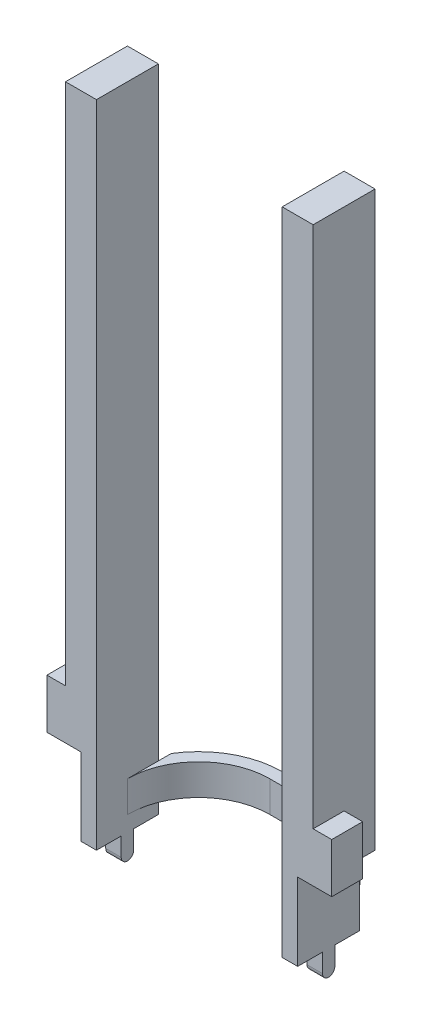
SolidWorks part; units mm, degrees
ref_plane "Front" through (0, 0, 0) normal (0, 0, 1) x (1, 0, 0)
ref_plane "Top" through (0, 0, 0) normal (0, 1, 0) x (1, 0, 0)
ref_plane "Right" through (0, 0, 0) normal (1, 0, 0) x (0, 0, -1)
sketch "草图2" plane through (0, 0, 0) normal (0, 1, 0) x (1, 0, 0)
  line L1 (-7, 23) -> (7, 23)
  line L4 (-7, 27) -> (7, 27)
  line L6 (-38.2984, -16) -> (-23.5227, -16) construction
  line L8 (-35.4759, -14) -> (-25.2483, -14) construction
  line L10 (25.2483, -14) -> (35.6561, -14) construction
  line L11 (23.5227, -16) -> (40.8516, -16) construction
  line L12 (-34, 0) -> (-30, 0)
  line L14 (30, 0) -> (34, 0)
  arc A4 (-7, 27) -> (-34, 0) centre (-7, 0) ccw
  arc A8 (-7, 23) -> (-30, 0) centre (-7, 0) ccw
  arc A10 (30, 0) -> (7, 23) centre (7, 0) ccw
  arc A11 (34, 0) -> (7, 27) centre (7, 0) ccw
  point P3 (0, 0)
  point P10 (0, 0)
extrude "凸台-拉伸1" add sketch "草图2" along normal blind 10
sketch "草图3" plane through (0, 10, 0) normal (0, 1, 0) x (1, 0, 0)
  line L1 (-30, 10) -> (-40, 10)
  line L2 (-30, 10) -> (-30, -10)
  line L3 (-30, -10) -> (-40, -10)
  line L4 (-40, 10) -> (-40, -10)
  line L5 (30, 10) -> (40, 10)
  line L6 (30, 10) -> (30, -10)
  line L7 (30, -10) -> (40, -10)
  line L8 (40, 10) -> (40, -10)
  dimension "D1" = 60
  dimension "D2" = 10
  dimension "D3" = 10
  dimension "D4" = 20
  dimension "D5" = 10
  dimension "D6" = 20
  dimension "D7" = 10
extrude "凸台-拉伸2" add sketch "草图3" along normal mid plane 30
sketch "草图4" plane through (40, 0, 0) normal (1, 0, 0) x (0, 0, -1)
  line L5 (-10, -5) -> (10, -5) construction
  line L6 (-2, -5) -> (2, -5)
  line L7 (-2, -5) -> (-2, -11)
  line L9 (2, -5) -> (2, -11)
  arc A1 (-2, -11) -> (2, -11) centre (0, -11) ccw
  dimension "D3" = 2
extrude "凸台-拉伸3" add sketch "草图4" against normal blind 10
sketch "草图5" plane through (-40, 0, 0) normal (-1, 0, 0) x (0, 0, 1)
  line L0 (-10, -5) -> (10, -5) construction
  line L14 (-2, -5) -> (2, -5)
  line L15 (-2, -5) -> (-2, -11)
  line L17 (2, -5) -> (2, -11)
  line L18 (0, 0) -> (0, -16.9384) construction
  arc A2 (-2, -11) -> (2, -11) centre (0, -11) ccw
  dimension "D3" = 2
extrude "凸台-拉伸4" add sketch "草图5" against normal blind 10
sketch "草图6" plane through (0, 25, 0) normal (0, 1, 0) x (1, 0, 0)
  line L1 (-40, 10) -> (-30, 10)
  line L2 (-40, 10) -> (-40, -10)
  line L3 (-40, -10) -> (-30, -10)
  line L4 (-30, 10) -> (-30, -10)
  line L5 (30, 10) -> (40, 10)
  line L6 (30, 10) -> (30, -10)
  line L7 (30, -10) -> (40, -10)
  line L8 (40, 10) -> (40, -10)
extrude "凸台-拉伸5" add sketch "草图6" along normal blind 180
sketch "草图7" plane through (0, -5, 0) normal (0, -1, 0) x (1, 0, 0)
  line L1 (-30, -10) -> (-40.3792, -10)
  line L2 (-30, -10) -> (-30, -20.8781)
  line L3 (-30, -20.8781) -> (-40.3792, -20.8781)
  line L4 (-40.3792, -10) -> (-40.3792, -20.8781)
  line L5 (30, -10) -> (37.1745, -10)
  line L6 (30, -10) -> (30, -21.5992)
  line L7 (30, -21.5992) -> (37.1745, -21.5992)
  line L8 (37.1745, -10) -> (37.1745, -21.5992)
extrude "切除-拉伸1" cut sketch "草图7" against normal through all
sketch "草图8" plane through (0, -5, 0) normal (0, -1, 0) x (1, 0, 0)
  line L0 (-30, -10) -> (-40, -10) construction
  line L1 (-40, 10) -> (-35, 10)
  line L2 (-40, 10) -> (-40, -10)
  line L3 (-40, -10) -> (-35, -10)
  line L4 (-35, 10) -> (-35, -10)
  line L5 (40, -10) -> (30, -10) construction
  line L6 (40, 10) -> (35, 10)
  line L7 (40, 10) -> (40, -10)
  line L8 (40, -10) -> (35, -10)
  line L9 (35, 10) -> (35, -10)
extrude "切除-拉伸2" cut sketch "草图8" against normal mid plane 50
sketch "草图9" plane through (0, 0, 10) normal (0, 0, 1) x (1, 0, 0)
  line L1 (40, 20) -> (46, 20)
  line L2 (40, 20) -> (40, 36)
  line L3 (40, 36) -> (46, 36)
  line L4 (46, 20) -> (46, 36)
  line L5 (-40, 20) -> (-46, 20)
  line L6 (-40, 20) -> (-40, 36)
  line L7 (-40, 36) -> (-46, 36)
  line L8 (-46, 20) -> (-46, 36)
  dimension "D1" = 16
  dimension "D2" = 6
  dimension "D3" = 16
  dimension "D4" = 6
extrude "凸台-拉伸6" add sketch "草图9" against normal blind 10
